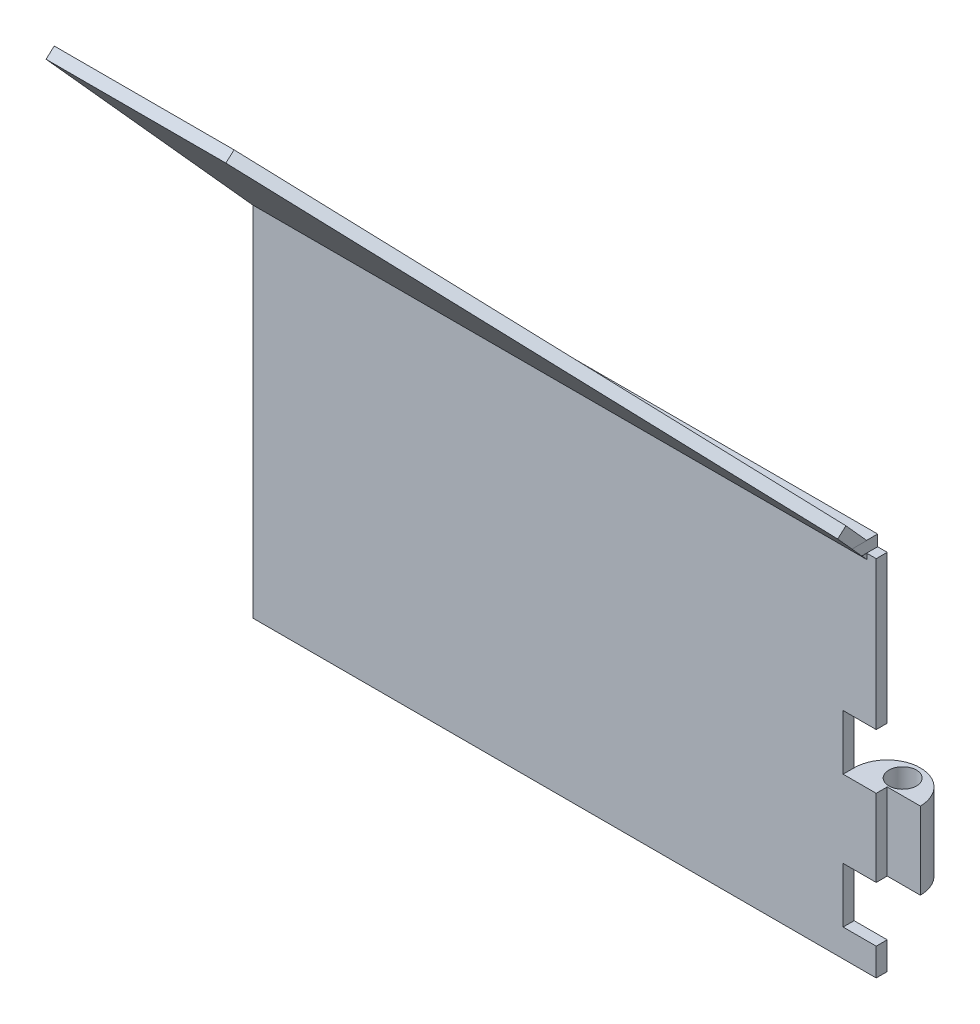
SolidWorks part; units mm, degrees
ref_plane "Front Plane" through (0, 0, 0) normal (0, 0, 1) x (1, 0, 0)
ref_plane "Top Plane" through (0, 0, 0) normal (0, 1, 0) x (1, 0, 0)
ref_plane "Right Plane" through (0, 0, 0) normal (1, 0, 0) x (0, 0, -1)
sketch "Sketch1" plane through (0, 0, 0) normal (0, 0, 1) x (1, 0, 0)
  line L0 (-28.25, -16.96) -> (-28.25, 16.96)
  line L1 (28.25, 16.96) -> (-28.25, 16.96)
  line L3 (28.25, -16.96) -> (28.25, -14.46)
  line L4 (28.25, -16.96) -> (-28.25, -16.96)
  line L7 (28.25, -14.46) -> (25.25, -14.46)
  line L8 (25.25, -14.46) -> (25.25, -9.46)
  line L9 (25.25, -9.46) -> (28.25, -9.46)
  line L10 (28.25, -9.46) -> (28.25, -2.46)
  line L11 (28.25, -2.46) -> (25.25, -2.46)
  line L12 (25.25, -2.46) -> (25.25, 2.54)
  line L13 (25.25, 2.54) -> (28.25, 2.54)
  line L14 (28.25, 2.54) -> (28.25, 16.96)
  line L15 (28.25, 2.54) -> (28.25, 16.96)
  point P2 (0, -16.96)
  point P6 (-28.25, 0)
  dimension "D2" = 33.92
  dimension "D3" = 56.5
  dimension "D7" = 2.5
  dimension "D8" = 5
  dimension "D9" = 7
  dimension "D10" = 3
extrude "Boss-Extrude1" add sketch "Sketch1" along normal blind 1 contours L15 L1 L0 L4 L3 L7 L8 L9 L10 L11 L12 L13
sketch "Sketch2" plane through (0, -9.46, 0) normal (0, -1, 0) x (1, 0, 0)
  line L0 (28.25, 0) -> (-28.25, 0) construction
  line L1 (25.25, 0) -> (28.25, 0)
  line L5 (28.25, 0) -> (31.25, 0)
  arc A0 (25.25, 0) -> (31.25, 0) centre (28.25, 0) ccw
  dimension "D1" = 3
sketch "Sketch4" plane through (-28.25, 0, 0) normal (-1, 0, 0) x (0, 0, 1)
  line L0 (0, 13.04) -> (-2.5, 10.54)
  line L2 (-2.5, 10.54) -> (-2.5, -14.46)
  line L3 (-2.5, -14.46) -> (0, -16.96)
  line L4 (0, -16.96) -> (0, 13.04)
  line L5 (0, -16.96) -> (0, 16.96) construction
  dimension "D1" = 135
  dimension "D2" = 25
  dimension "D3" = 2.5
extrude "Boss-Extrude3" add sketch "Sketch4" against normal blind 50
extrude "Boss-Extrude6" add sketch "Sketch2" against normal up to surface (7 mm away) up to face at (26.75, -2.46, 0.5)
sketch "Sketch8" plane through (0, -2.46, 0) normal (0, 1, 0) x (1, 0, 0)
  line L0 (28.25, -1) -> (28.25, 0) construction
  circle A0 centre (28.25, 1.4) radius 1.25
  arc A1 (31.25, 0) -> (25.25, 0) centre (28.25, 0) ccw construction
  dimension "D1" = 2.5
  dimension "D2" = 1.4
extrude "Cut-Extrude3" cut sketch "Sketch8" against normal up to surface (7 mm away) up to face at (27.65, -9.46, -0.2)
ref_plane "Plane1" through (0, 7.0963, -7.8813) normal (0, 0.6691, -0.7431) x (-1, 0, 0)
sketch "Sketch5" plane through (0, 7.0963, -7.8813) normal (0, 0.6691, -0.7431) x (-1, 0, 0)
  line L0 (28.25, 13.2729) -> (28.25, 40.1837)
  line L1 (28.25, 40.1837) -> (11.95, 40.1837)
  line L2 (11.95, 40.1837) -> (-27.4, 16.1037)
  line L3 (-27.4, 13.2729) -> (28.25, 13.2729)
  line L4 (28.25, 13.2729) -> (28.25, 12.6037) construction
  line L5 (-28.25, 2.5567) -> (-28.25, 13.2729) construction
  line L6 (-28.25, 13.2729) -> (28.25, 13.2729) construction
  line L7 (-27.4, 16.1037) -> (-27.4, 13.2729)
  line L8 (-28.25, 12.6037) -> (28.25, 12.6037) construction
  dimension "D1" = 16.3
  dimension "D2" = 27.58
  dimension "D3" = 3.5
  dimension "D4" = 0.85
extrude "Boss-Extrude4" add sketch "Sketch5" against normal blind 1 separate body
sketch "Sketch6" plane through (0, 9.8637, 8.8813) normal (0, -0.7431, -0.6691) x (-1, 0, 0)
  line L4 (28.25, 10.6053) -> (-27.4, 10.6053)
  line L5 (28.25, 9.6053) -> (28.25, 10.6053)
  line L6 (-27.4, 9.6053) -> (28.25, 9.6053)
  line L7 (-27.4, 10.6053) -> (-27.4, 9.6053)
  line L8 (28.25, 10.6053) -> (-27.4, 10.6053)
  line L9 (28.25, 9.6053) -> (28.25, 10.6053)
  line L10 (-27.4, 9.6053) -> (28.25, 9.6053)
  line L11 (-27.4, 10.6053) -> (-27.4, 9.6053)
  dimension "D1" = 0
extrude "Boss-Extrude5" add sketch "Sketch6" along normal up to surface (1.4945 mm away)
sketch "Sketch7" plane through (0, 0, 0) normal (0, 0, 1) x (1, 0, 0)
  line L1 (28.25, 16.96) -> (27.38, 16.96)
  line L2 (28.25, 16.96) -> (28.25, 15.96)
  line L3 (28.25, 15.96) -> (27.38, 15.96)
  line L4 (27.38, 16.96) -> (27.38, 15.96)
  dimension "D1" = 0.87
  dimension "D2" = 1
extrude "Cut-Extrude2" cut sketch "Sketch7" against normal up to surface (2.3456 mm away)
